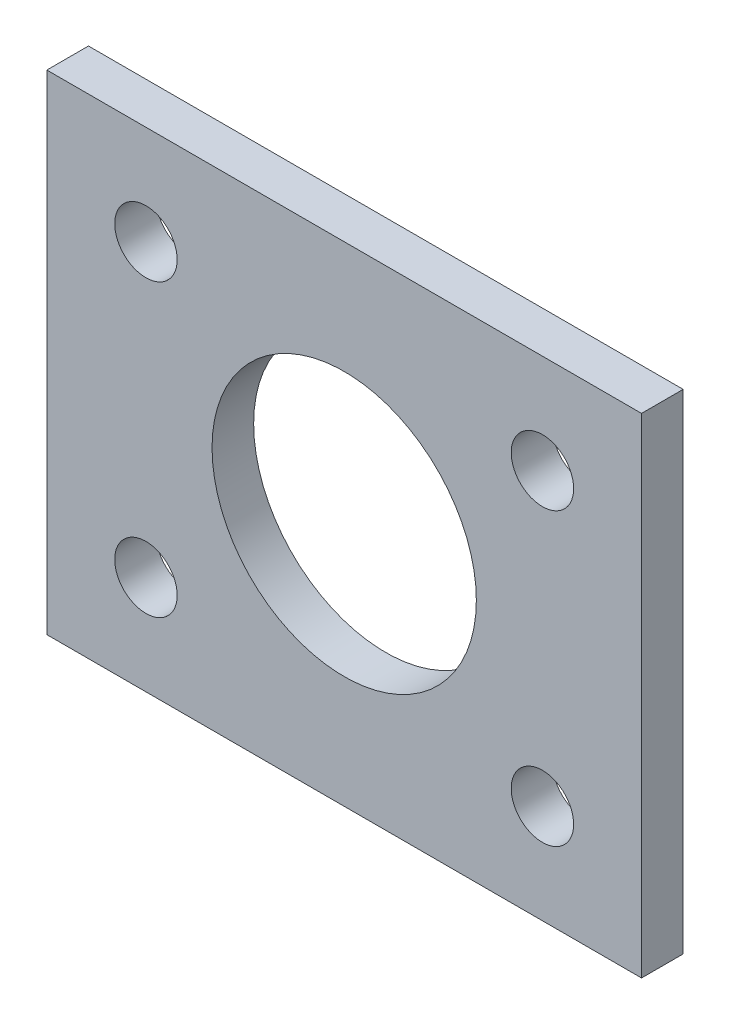
SolidWorks part; units mm, degrees
ref_plane "Front Plane" through (0, 0, 0) normal (0, 0, 1) x (1, 0, 0)
ref_plane "Top Plane" through (0, 0, 0) normal (0, 1, 0) x (1, 0, 0)
ref_plane "Right Plane" through (0, 0, 0) normal (1, 0, 0) x (0, 0, -1)
sketch "Sketch5" plane through (0, 0, 0) normal (0, 0, 1) x (1, 0, 0)
  line L0 (-9.525, -6.985) -> (9.525, -6.985) construction
  line L1 (-14.2875, 11.7475) -> (14.2875, 11.7475)
  line L2 (-14.2875, 11.7475) -> (-14.2875, -11.7475)
  line L3 (-14.2875, -11.7475) -> (14.2875, -11.7475)
  line L4 (14.2875, 11.7475) -> (14.2875, -11.7475)
  line L5 (-14.2875, 11.7475) -> (14.2875, -11.7475) construction
  line L6 (-14.2875, -11.7475) -> (14.2875, 11.7475) construction
  line L7 (9.525, -6.985) -> (9.525, 6.985) construction
  line L8 (9.525, 6.985) -> (-9.525, 6.985) construction
  line L9 (-9.525, 6.985) -> (-9.525, -6.985) construction
  circle A0 centre (-9.525, 6.985) radius 1.5
  circle A1 centre (9.525, 6.985) radius 1.5
  circle A2 centre (-9.525, -6.985) radius 1.5
  circle A3 centre (9.525, -6.985) radius 1.5
  circle A4 centre (0, 0) radius 6.35
  point P0 (0, 0)
  point P14 (-9.525, 0)
  point P16 (0, 6.985)
  dimension "D1" = 3
  dimension "D6" = 12.7
  dimension "D2" = 19.05
  dimension "D3" = 4.7625
  dimension "D4" = 6.985
  dimension "D5" = 4.7625
extrude "Boss-Extrude1" add sketch "Sketch5" along normal blind 2
equation "\"bottomThickness\"= .220in"
equation "\"wallThickness\"= .125in"
